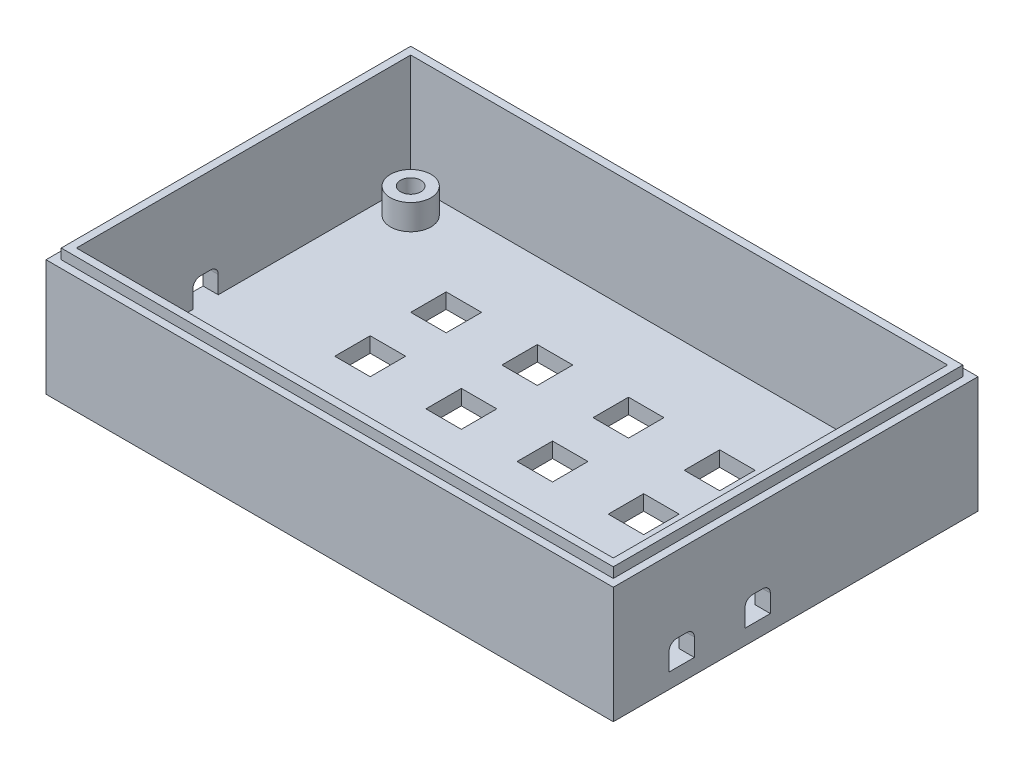
SolidWorks part; units mm, degrees
ref_plane "Plano frontal" through (0, 0, 0) normal (0, 0, 1) x (1, 0, 0)
ref_plane "Plano superior" through (0, 0, 0) normal (0, 1, 0) x (1, 0, 0)
ref_plane "Plano direito" through (0, 0, 0) normal (1, 0, 0) x (0, 0, -1)
sketch "Sketch1" plane through (0, 0, 0) normal (0, 1, 0) x (1, 0, 0)
  line L0 (53, 33) -> (-53, -33) construction
  line L1 (-53, 33) -> (53, 33)
  line L2 (-53, 33) -> (-53, -33)
  line L3 (-53, -33) -> (53, -33)
  line L4 (53, 33) -> (53, -33)
  line L5 (0, 0) -> (0, 33) construction
  line L6 (0, 0) -> (-53, 0) construction
  circle A0 centre (-47.6, 27.6) radius 2
  circle A1 centre (47.6, 27.6) radius 2
  circle A2 centre (47.6, -27.6) radius 2
  circle A3 centre (-47.6, -27.6) radius 2
  point P7 (-47.6, 29.6)
  point P8 (-49.6, 27.6)
  dimension "D3" = 4
  dimension "D1" = 106
  dimension "D2" = 66
  dimension "D4" = 3.4
  dimension "D5" = 3.4
extrude "Boss-Extrude1" add sketch "Sketch1" along normal blind 3
sketch "Sketch2" plane through (0, 3, 0) normal (0, 1, 0) x (1, 0, 0)
  line L0 (-56, 36) -> (-56, -36)
  line L1 (-56, -36) -> (56, -36)
  line L2 (56, -36) -> (56, 36)
  line L3 (56, 36) -> (-56, 36)
  line L4 (-53, 33) -> (-53, -33)
  line L5 (-53, -33) -> (53, -33)
  line L6 (53, -33) -> (53, 33)
  line L7 (53, 33) -> (-53, 33)
  line L8 (-53, 33) -> (-53, -33)
  line L9 (-53, -33) -> (53, -33)
  line L10 (53, -33) -> (53, 33)
  line L11 (53, 33) -> (-53, 33)
  dimension "D1" = 0
  dimension "D2" = 3
extrude "Boss-Extrude2" add sketch "Sketch2" along normal blind 20 and the other way blind 3
sketch "Sketch4" plane through (0, 23, 0) normal (0, 1, 0) x (1, 0, 0)
  line L0 (-54.5, 34.5) -> (-54.5, -34.5)
  line L1 (-53, 33) -> (53, 33)
  line L2 (-53, 33) -> (-53, -33)
  line L3 (-53, -33) -> (53, -33)
  line L4 (53, 33) -> (53, -33)
  line L5 (-54.5, -34.5) -> (54.5, -34.5)
  line L6 (54.5, 34.5) -> (54.5, -34.5)
  line L7 (-54.5, 34.5) -> (54.5, 34.5)
  dimension "D1" = 1.5
extrude "Boss-Extrude3" add sketch "Sketch4" along normal blind 2
sketch "Sketch5" plane through (53, 0, 0) normal (-1, 0, 0) x (0, 0, 1)
  line L0 (33, 3) -> (-33, 3) construction
  line L1 (5, 3) -> (10, 3)
  line L2 (5, 3) -> (5, 6.5)
  line L3 (6.5, 8) -> (8.5, 8)
  line L4 (10, 3) -> (10, 6.5)
  line L5 (33, 3) -> (33, 25) construction
  line L6 (20, 3) -> (25, 3)
  line L7 (20, 3) -> (20, 6.5)
  line L8 (21.5, 8) -> (23.5, 8)
  line L9 (25, 3) -> (25, 6.5)
  arc A0 (25, 6.5) -> (23.5, 8) centre (23.5, 6.5) ccw
  arc A1 (20, 6.5) -> (21.5, 8) centre (21.5, 6.5) cw
  arc A2 (8.5, 8) -> (10, 6.5) centre (8.5, 6.5) cw
  arc A3 (5, 6.5) -> (6.5, 8) centre (6.5, 6.5) cw
  point P14 (25, 8)
  point P17 (20, 8)
  point P20 (10, 8)
  point P23 (5, 8)
  dimension "D7" = 1.5
  dimension "D1" = 5
  dimension "D2" = 5
  dimension "D3" = 5
  dimension "D4" = 5
  dimension "D5" = 8
  dimension "D6" = 10
extrude "Cut-Extrude1" cut sketch "Sketch5" against normal through all
sketch "Sketch6" plane through (0, 3, 0) normal (0, 1, 0) x (1, 0, 0)
  line L0 (0, 0) -> (0, 33) construction
  line L1 (53, 33) -> (-53, 33) construction
  line L2 (-53, 0) -> (0, 0) construction
  line L3 (-53, 33) -> (-53, -33) construction
  circle A0 centre (-47.6, 27.6) radius 4
  circle A1 centre (-47.6, 27.6) radius 2
  circle A2 centre (47.6, 27.6) radius 2
  circle A3 centre (47.6, 27.6) radius 4
  circle A4 centre (47.6, -27.6) radius 4
  circle A5 centre (47.6, -27.6) radius 2
  circle A6 centre (-47.6, -27.6) radius 2
  circle A7 centre (-47.6, -27.6) radius 4
  dimension "D1" = 8
extrude "Boss-Extrude4" add sketch "Sketch6" along normal blind 5
sketch "Sketch7" plane through (0, 3, 0) normal (0, 1, 0) x (1, 0, 0)
  line L0 (53, 33) -> (-53, 33) construction
  line L1 (-53, 33) -> (-53, -33) construction
  line L2 (-13, 18) -> (-6, 18)
  line L3 (-31, 18) -> (-24, 18)
  line L4 (-31, 18) -> (-31, 11)
  line L5 (-31, 11) -> (-24, 11)
  line L6 (-24, 18) -> (-24, 11)
  line L7 (-13, 18) -> (-13, 11)
  line L8 (-13, 11) -> (-6, 11)
  line L9 (-6, 18) -> (-6, 11)
  line L10 (5, 18) -> (12, 18)
  line L11 (5, 18) -> (5, 11)
  line L12 (5, 11) -> (12, 11)
  line L13 (12, 18) -> (12, 11)
  line L14 (23, 18) -> (30, 18)
  line L15 (23, 18) -> (23, 11)
  line L16 (23, 11) -> (30, 11)
  line L17 (30, 18) -> (30, 11)
  line L18 (-13, 3) -> (-6, 3)
  line L19 (-13, 3) -> (-13, -4)
  line L20 (-13, -4) -> (-6, -4)
  line L21 (-6, 3) -> (-6, -4)
  line L22 (5, 3) -> (12, 3)
  line L23 (5, 3) -> (5, -4)
  line L24 (5, -4) -> (12, -4)
  line L25 (12, 3) -> (12, -4)
  line L26 (23, 3) -> (30, 3)
  line L27 (23, 3) -> (23, -4)
  line L28 (23, -4) -> (30, -4)
  line L29 (30, 3) -> (30, -4)
  line L30 (-13, -12) -> (-6, -12)
  line L31 (-13, -12) -> (-13, -19)
  line L32 (-13, -19) -> (-6, -19)
  line L33 (-6, -12) -> (-6, -19)
  line L34 (5, -12) -> (12, -12)
  line L35 (5, -12) -> (5, -19)
  line L36 (5, -19) -> (12, -19)
  line L37 (12, -12) -> (12, -19)
  line L38 (23, -12) -> (30, -12)
  line L39 (23, -12) -> (23, -19)
  line L40 (23, -19) -> (30, -19)
  line L41 (30, -12) -> (30, -19)
  line L42 (-31, 3) -> (-24, 3)
  line L43 (-31, 3) -> (-31, -4)
  line L44 (-31, -4) -> (-24, -4)
  line L45 (-24, 3) -> (-24, -4)
  line L46 (-31, -12) -> (-24, -12)
  line L47 (-31, -12) -> (-31, -19)
  line L48 (-31, -19) -> (-24, -19)
  line L49 (-24, -12) -> (-24, -19)
  dimension "D1" = 7
  dimension "D2" = 7
  dimension "D3" = 15
  dimension "D4" = 22
extrude "Cut-Extrude2" cut sketch "Sketch7" against normal through all
mirror "Mirror1" about plane through (0, 0, 0) normal (1, 0, 0) of "Cut-Extrude1"
